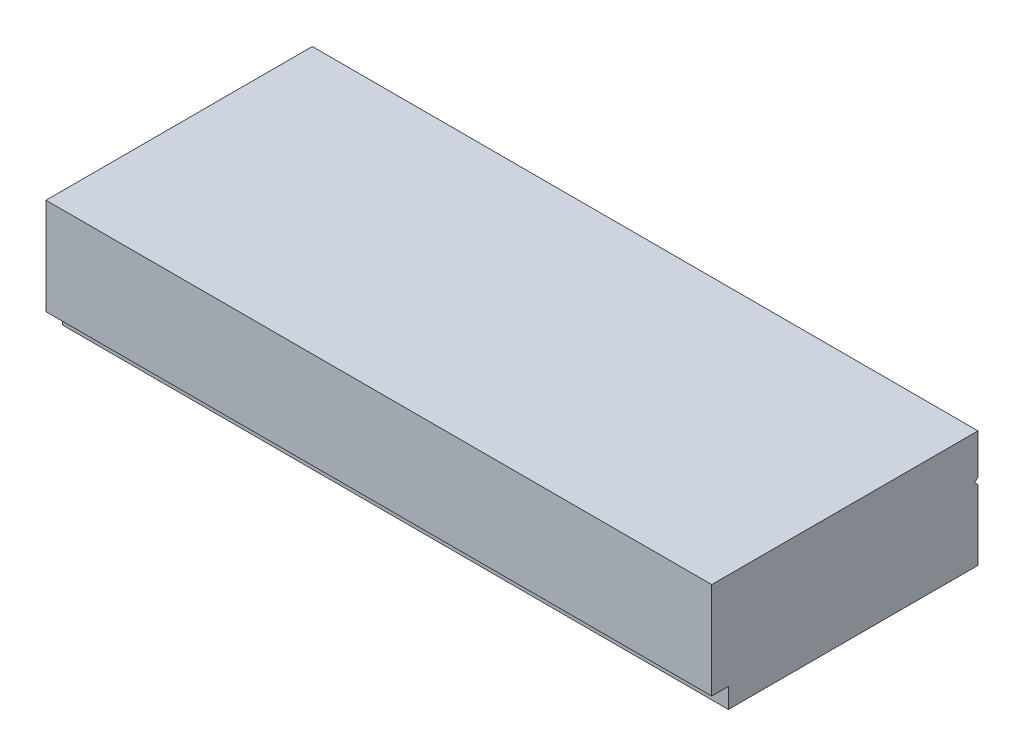
SolidWorks part; units mm, degrees
ref_plane "Front Plane" through (0, 0, 0) normal (0, 0, 1) x (1, 0, 0)
ref_plane "Top Plane" through (0, 0, 0) normal (0, 1, 0) x (1, 0, 0)
ref_plane "Right Plane" through (0, 0, 0) normal (1, 0, 0) x (0, 0, -1)
sketch "Sketch1" plane through (0, 0, 0) normal (0, 1, 0) x (1, 0, 0)
  line L1 (-100, -40) -> (100, -40)
  line L2 (-100, -40) -> (-100, 40)
  line L3 (-100, 40) -> (100, 40)
  line L4 (100, -40) -> (100, 40)
  line L5 (-100, -40) -> (100, 40) construction
  line L6 (-100, 40) -> (100, -40) construction
  point P0 (0, 0)
  dimension "D1" = 80
  dimension "D2" = 200
extrude "Boss-Extrude1" add sketch "Sketch1" along normal blind 35
sketch "Sketch2" plane through (-100, 0, 0) normal (-1, 0, 0) x (0, 0, 1)
  line L1 (40, 0) -> (35, 0)
  line L2 (40, 0) -> (40, 6)
  line L3 (40, 6) -> (35, 6)
  line L4 (35, 0) -> (35, 6)
  dimension "D1" = 6
  dimension "D2" = 5
extrude "Cut-Extrude1" cut sketch "Sketch2" against normal through all
sketch "Sketch3" plane through (0, 0, 0) normal (1, 0, 0) x (0, 0, -1)
  line L0 (40, 3) -> (39.4226, 2)
  line L1 (40, 35) -> (40, 0) construction
  line L2 (39.4226, 2) -> (40, 1)
  line L3 (40, 1) -> (40, 3)
  line L4 (44, 0) -> (-44, 0) construction
  dimension "D1" = 2
  dimension "D2" = 1
  dimension "D3" = 120
  dimension "D4" = 1
sketch "Sketch4" [suppressed] plane through (0, 35, 0) normal (0, 1, 0) x (1, 0, 0)
  line L0 (100, 40) -> (-100, 40) construction
  line L1 (100, -40) -> (100, 40) construction
  circle A0 centre (-62, 40) radius 31
  circle A1 centre (38, 40) radius 55
  dimension "D2" = 110
  dimension "D3" = 62
  dimension "D1" = 100
  dimension "D4" = 62
extrude "Cut-Extrude3" [suppressed] cut sketch "Sketch4" against normal up to surface (35 mm away)
sketch "Sketch5" [suppressed] plane through (0, 35, 0) normal (0, 1, 0) x (1, 0, 0)
  line L0 (100, 40) -> (-100, 40) construction
  line L1 (-100, 40) -> (-100, -40) construction
  circle A0 centre (-38, 40) radius 55
  circle A1 centre (62, 40) radius 31
  dimension "D2" = 110
  dimension "D3" = 62
  dimension "D1" = 100
  dimension "D4" = 62
extrude "Cut-Extrude4" [suppressed] cut sketch "Sketch5" against normal up to surface (35 mm away)
sketch "Sketch6" plane through (100, 0, 0) normal (1, 0, 0) x (0, 0, -1)
  line L0 (40, 22) -> (40, 23)
  line L1 (40, 35) -> (40, 0) construction
  line L2 (40, 23) -> (39, 22)
  line L3 (39, 22) -> (40, 21)
  line L4 (40, 21) -> (40, 22)
  line L5 (40, 35) -> (40, 0) construction
  point P8 (40, 17.5)
  dimension "D1" = 1
  dimension "D2" = 45
  dimension "D3" = 45
  dimension "D4" = 4.5
extrude "Cut-Extrude5" cut sketch "Sketch6" against normal through all
sketch "Sketch7" [suppressed] plane through (0, 35, 0) normal (0, 1, 0) x (1, 0, 0)
  point P0 (-87, -22)
  point P1 (-67, -22)
  point P3 (0, -22)
  point P5 (87, -22)
hole_wizard "Ø12.0mm Dowel Hole1" [suppressed] positions "Sketch8" profile "Sketch9" hole size "Ø12.0" standard "ISO"
sketch "Sketch8" plane through (0, 35, 0) normal (0, 1, 0) x (1, 0, 0)
  point P0 (-87, -22)
  point P3 (0, -22)
  point P6 (87, -22)
sketch "Sketch9" plane through (-87, 35, 22) normal (1, 0, 0) x (0, 0, 1)
  line L0 (0, 0) -> (0, 28.0644)
  line L1 (0, 28.0644) -> (5.1, 25)
  line L2 (5.1, 25) -> (5.1, 0)
  line L5 (5.1, 0) -> (0, 0)
  line L10 (0, 28.0644) -> (-5.1, 25) construction
  line L11 (0, -6.35) -> (0, 107.95) construction
  dimension "Hole Dia." = 10.2
  dimension "Hole Depth" = 25
  dimension "Drill Angle" = 118
hole_wizard "Ø6.0mm Dowel Hole1" [suppressed] positions "Sketch10" profile "Sketch11" hole size "Ø6.0" standard "ISO"
sketch "Sketch10" plane through (0, 35, 0) normal (0, 1, 0) x (1, 0, 0)
  point P0 (-67, -22)
sketch "Sketch11" plane through (-67, 35, 22) normal (1, 0, 0) x (0, 0, 1)
  line L0 (0, 0) -> (0, 11.8026)
  line L1 (0, 11.8026) -> (3, 10)
  line L2 (3, 10) -> (3, 0)
  line L5 (3, 0) -> (0, 0)
  line L10 (0, 11.8026) -> (-3, 10) construction
  line L11 (0, -6.35) -> (0, 107.95) construction
  dimension "Hole Dia." = 6
  dimension "Hole Depth" = 10
  dimension "Drill Angle" = 118
sketch "Sketch12" [suppressed] plane through (0, 35, 0) normal (0, 1, 0) x (1, 0, 0)
  point P0 (-87, -22)
  point P1 (0, -22)
  point P3 (67, -22)
  point P5 (87, -22)
hole_wizard "Ø12.0mm Dowel Hole2" [suppressed] positions "Sketch13" profile "Sketch14" hole size "Ø12.0" standard "ISO"
sketch "Sketch13" plane through (0, 35, 0) normal (0, 1, 0) x (1, 0, 0)
  point P0 (-87, -22)
  point P3 (0, -22)
  point P6 (87, -22)
sketch "Sketch14" plane through (-87, 35, 22) normal (1, 0, 0) x (0, 0, 1)
  line L0 (0, 0) -> (0, 28.0644)
  line L1 (0, 28.0644) -> (5.1, 25)
  line L2 (5.1, 25) -> (5.1, 0)
  line L5 (5.1, 0) -> (0, 0)
  line L10 (0, 28.0644) -> (-5.1, 25) construction
  line L11 (0, -6.35) -> (0, 107.95) construction
  dimension "Hole Dia." = 10.2
  dimension "Hole Depth" = 25
  dimension "Drill Angle" = 118
hole_wizard "Ø6.0mm Dowel Hole2" [suppressed] positions "Sketch15" profile "Sketch16" hole size "Ø6.0" standard "ISO"
sketch "Sketch15" plane through (0, 35, 0) normal (0, 1, 0) x (1, 0, 0)
  point P0 (67, -22)
sketch "Sketch16" plane through (67, 35, 22) normal (1, 0, 0) x (0, 0, 1)
  line L0 (0, 0) -> (0, 11.8026)
  line L1 (0, 11.8026) -> (3, 10)
  line L2 (3, 10) -> (3, 0)
  line L5 (3, 0) -> (0, 0)
  line L10 (0, 11.8026) -> (-3, 10) construction
  line L11 (0, -6.35) -> (0, 107.95) construction
  dimension "Hole Dia." = 6
  dimension "Hole Depth" = 10
  dimension "Drill Angle" = 118
chamfer "Chamfer1" [suppressed] distance 3.5 angle 45
chamfer "Chamfer2" [suppressed] distance 3.5 angle 45
